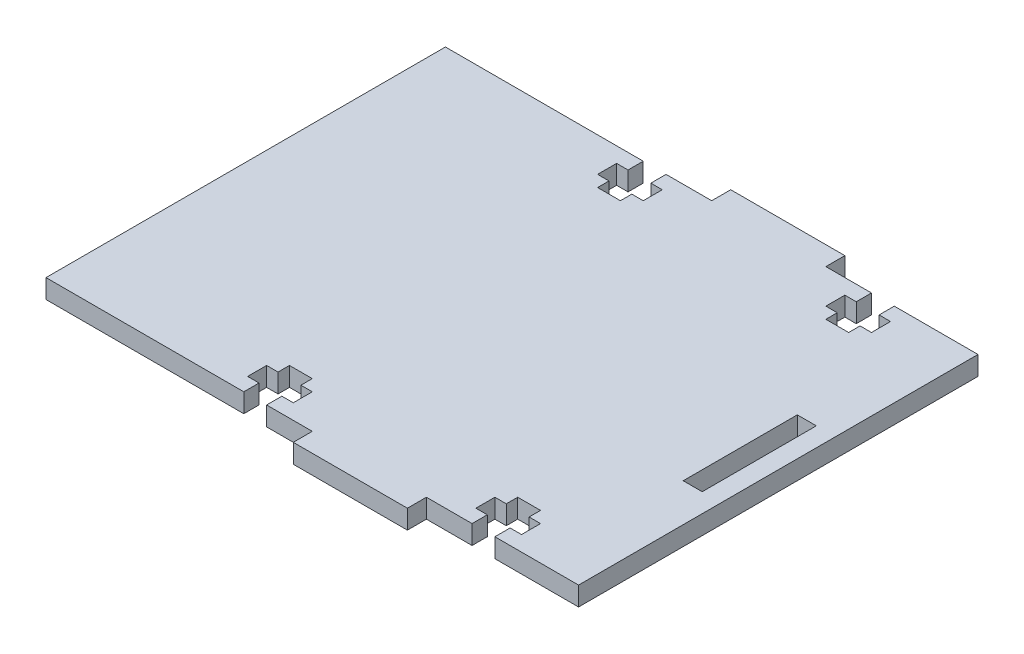
SolidWorks part; units mm, degrees
ref_plane "Front Plane" through (0, 0, 0) normal (0, 0, 1) x (1, 0, 0)
ref_plane "Top Plane" through (0, 0, 0) normal (0, 1, 0) x (1, 0, 0)
ref_plane "Right Plane" through (0, 0, 0) normal (1, 0, 0) x (0, 0, -1)
sketch "Sketch1" plane through (0, 0, 0) normal (0, 1, 0) x (1, 0, 0)
  line L0 (88.9, 33.3375) -> (85.725, 33.3375) construction
  line L1 (0, 0) -> (88.9, 0)
  line L2 (0, 0) -> (0, 66.675)
  line L3 (0, 66.675) -> (88.9, 66.675)
  line L4 (88.9, 0) -> (88.9, 66.675)
  line L5 (85.725, 42.8625) -> (82.55, 42.8625)
  line L6 (85.725, 42.8625) -> (85.725, 23.8125)
  line L7 (85.725, 23.8125) -> (82.55, 23.8125)
  line L8 (82.55, 42.8625) -> (82.55, 23.8125)
  line L9 (82.55, 42.8625) -> (82.55, 66.675) construction
  line L10 (82.55, 66.675) -> (63.5, 66.675)
  line L11 (82.55, 66.675) -> (82.55, 69.85)
  line L12 (82.55, 69.85) -> (63.5, 69.85)
  line L13 (63.5, 66.675) -> (63.5, 69.85)
  line L14 (63.5, 66.675) -> (44.45, 66.675)
  line L15 (63.5, 66.675) -> (63.5, 69.85)
  line L16 (63.5, 69.85) -> (44.45, 69.85)
  line L17 (44.45, 66.675) -> (44.45, 69.85)
  line L18 (44.45, 66.675) -> (25.4, 66.675)
  line L19 (44.45, 66.675) -> (44.45, 69.85)
  line L20 (44.45, 69.85) -> (25.4, 69.85)
  line L21 (25.4, 66.675) -> (25.4, 69.85)
  line L22 (25.4, 66.675) -> (6.35, 66.675)
  line L23 (25.4, 66.675) -> (25.4, 69.85)
  line L24 (25.4, 69.85) -> (6.35, 69.85)
  line L25 (6.35, 66.675) -> (6.35, 69.85)
  line L26 (6.35, 0) -> (6.35, -3.175)
  line L27 (6.35, 66.675) -> (6.35, 69.85)
  line L28 (6.35, 0) -> (6.35, -3.175)
  line L29 (25.4, -3.175) -> (6.35, -3.175)
  line L30 (25.4, 0) -> (25.4, -3.175)
  line L31 (25.4, 0) -> (6.35, 0)
  line L32 (25.4, 0) -> (25.4, -3.175)
  line L33 (44.45, -3.175) -> (25.4, -3.175)
  line L34 (44.45, 0) -> (44.45, -3.175)
  line L35 (44.45, 0) -> (25.4, 0)
  line L36 (44.45, 0) -> (44.45, -3.175)
  line L37 (63.5, -3.175) -> (44.45, -3.175)
  line L38 (63.5, 0) -> (63.5, -3.175)
  line L39 (63.5, 0) -> (44.45, 0)
  line L40 (63.5, 0) -> (63.5, -3.175)
  line L41 (82.55, -3.175) -> (63.5, -3.175)
  line L42 (82.55, 0) -> (82.55, -3.175)
  line L43 (82.55, 0) -> (63.5, 0)
  line L44 (34.925, 69.85) -> (34.925, 66.675) construction
  line L45 (34.925, 59.055) -> (34.925, 66.675) construction
  line L46 (33.02, 59.055) -> (33.02, 60.96)
  line L47 (33.02, 60.96) -> (31.115, 60.96)
  line L48 (31.115, 60.96) -> (31.115, 64.135)
  line L49 (31.115, 64.135) -> (33.02, 64.135)
  line L50 (33.02, 64.135) -> (33.02, 66.675)
  line L51 (33.02, 66.675) -> (36.83, 66.675)
  line L52 (36.83, 64.135) -> (36.83, 66.675)
  line L53 (38.735, 64.135) -> (36.83, 64.135)
  line L54 (38.735, 60.96) -> (38.735, 64.135)
  line L55 (36.83, 60.96) -> (38.735, 60.96)
  line L56 (36.83, 59.055) -> (36.83, 60.96)
  line L57 (33.02, 59.055) -> (36.83, 59.055)
  line L58 (33.02, 59.055) -> (33.02, 60.96)
  line L59 (53.975, 69.85) -> (53.975, -3.175) construction
  line L60 (0, 33.3375) -> (34.925, 33.3375) construction
  line L61 (33.02, 60.96) -> (31.115, 60.96)
  line L62 (31.115, 60.96) -> (31.115, 64.135)
  line L63 (31.115, 64.135) -> (33.02, 64.135)
  line L64 (33.02, 64.135) -> (33.02, 66.675)
  line L65 (36.83, 64.135) -> (36.83, 66.675)
  line L66 (38.735, 64.135) -> (36.83, 64.135)
  line L67 (38.735, 60.96) -> (38.735, 64.135)
  line L68 (36.83, 60.96) -> (38.735, 60.96)
  line L69 (36.83, 59.055) -> (36.83, 60.96)
  line L70 (73.025, 59.055) -> (73.025, 66.675) construction
  line L71 (73.025, 69.85) -> (73.025, 66.675) construction
  line L72 (71.12, 59.055) -> (71.12, 60.96)
  line L73 (71.12, 60.96) -> (69.215, 60.96)
  line L74 (69.215, 60.96) -> (69.215, 64.135)
  line L75 (69.215, 64.135) -> (71.12, 64.135)
  line L76 (71.12, 64.135) -> (71.12, 66.675)
  line L77 (74.93, 64.135) -> (74.93, 66.675)
  line L78 (76.835, 64.135) -> (74.93, 64.135)
  line L79 (76.835, 60.96) -> (76.835, 64.135)
  line L80 (74.93, 60.96) -> (76.835, 60.96)
  line L81 (74.93, 59.055) -> (74.93, 60.96)
  line L82 (74.93, 59.055) -> (71.12, 59.055)
  line L83 (71.12, 59.055) -> (71.12, 60.96)
  line L84 (71.12, 60.96) -> (69.215, 60.96)
  line L85 (69.215, 60.96) -> (69.215, 64.135)
  line L86 (69.215, 64.135) -> (71.12, 64.135)
  line L87 (71.12, 64.135) -> (71.12, 66.675)
  line L88 (74.93, 66.675) -> (71.12, 66.675)
  line L89 (74.93, 64.135) -> (74.93, 66.675)
  line L90 (76.835, 64.135) -> (74.93, 64.135)
  line L91 (76.835, 60.96) -> (76.835, 64.135)
  line L92 (74.93, 60.96) -> (76.835, 60.96)
  line L93 (74.93, 59.055) -> (74.93, 60.96)
  line L94 (34.925, 7.62) -> (34.925, 0) construction
  line L95 (34.925, -3.175) -> (34.925, 0) construction
  line L96 (36.83, 7.62) -> (36.83, 5.715)
  line L97 (36.83, 5.715) -> (38.735, 5.715)
  line L98 (38.735, 5.715) -> (38.735, 2.54)
  line L99 (38.735, 2.54) -> (36.83, 2.54)
  line L100 (36.83, 2.54) -> (36.83, 0)
  line L101 (33.02, 2.54) -> (33.02, 0)
  line L102 (31.115, 2.54) -> (33.02, 2.54)
  line L103 (31.115, 5.715) -> (31.115, 2.54)
  line L104 (33.02, 5.715) -> (31.115, 5.715)
  line L105 (33.02, 7.62) -> (33.02, 5.715)
  line L106 (33.02, 7.62) -> (36.83, 7.62)
  line L107 (36.83, 7.62) -> (36.83, 5.715)
  line L108 (36.83, 5.715) -> (38.735, 5.715)
  line L109 (38.735, 5.715) -> (38.735, 2.54)
  line L110 (38.735, 2.54) -> (36.83, 2.54)
  line L111 (36.83, 2.54) -> (36.83, 0)
  line L112 (33.02, 0) -> (36.83, 0)
  line L113 (33.02, 2.54) -> (33.02, 0)
  line L114 (31.115, 2.54) -> (33.02, 2.54)
  line L115 (31.115, 5.715) -> (31.115, 2.54)
  line L116 (33.02, 5.715) -> (31.115, 5.715)
  line L117 (33.02, 7.62) -> (33.02, 5.715)
  line L118 (73.025, -3.175) -> (73.025, 0) construction
  line L119 (73.025, 7.62) -> (73.025, 0) construction
  line L120 (74.93, 7.62) -> (74.93, 5.715)
  line L121 (74.93, 5.715) -> (76.835, 5.715)
  line L122 (76.835, 5.715) -> (76.835, 2.54)
  line L123 (76.835, 2.54) -> (74.93, 2.54)
  line L124 (74.93, 2.54) -> (74.93, 0)
  line L125 (74.93, 0) -> (71.12, 0)
  line L126 (71.12, 2.54) -> (71.12, 0)
  line L127 (69.215, 2.54) -> (71.12, 2.54)
  line L128 (69.215, 5.715) -> (69.215, 2.54)
  line L129 (71.12, 5.715) -> (69.215, 5.715)
  line L130 (71.12, 7.62) -> (71.12, 5.715)
  line L131 (74.93, 7.62) -> (71.12, 7.62)
  line L132 (74.93, 7.62) -> (74.93, 5.715)
  line L133 (74.93, 5.715) -> (76.835, 5.715)
  line L134 (76.835, 5.715) -> (76.835, 2.54)
  line L135 (76.835, 2.54) -> (74.93, 2.54)
  line L136 (74.93, 2.54) -> (74.93, 0)
  line L137 (71.12, 2.54) -> (71.12, 0)
  line L138 (69.215, 2.54) -> (71.12, 2.54)
  line L139 (69.215, 5.715) -> (69.215, 2.54)
  line L140 (71.12, 5.715) -> (69.215, 5.715)
  line L141 (71.12, 7.62) -> (71.12, 5.715)
  dimension "D1" = 66.675
  dimension "D2" = 88.9
  dimension "D3" = 3.175
  dimension "D4" = 19.05
  dimension "D5" = 3.175
  dimension "D6" = 19.05
  dimension "D7" = 3.175
  dimension "D8" = 6.35
  dimension "D9" = 2.54
  dimension "D10" = 7.62
  dimension "D11" = 3.175
  dimension "D12" = 1.905
  dimension "D13" = 3.81
extrude "Boss-Extrude3" add sketch "Sketch1" along normal blind 3.175 contours L131 L120 L121 L122 L123 L124 L43 L1 L4 L3 L77 L78 L79 L80 L81 L82 L72 L73 L74 L75 L76 L52 L53 L54 L55 L56 L57 L46 L47 L48 L49 L50 L2 L101 L102 L103 L104 L105 L106 L96 L97 | L38 L1 L34 L37 | L17 L3 L13 L16
